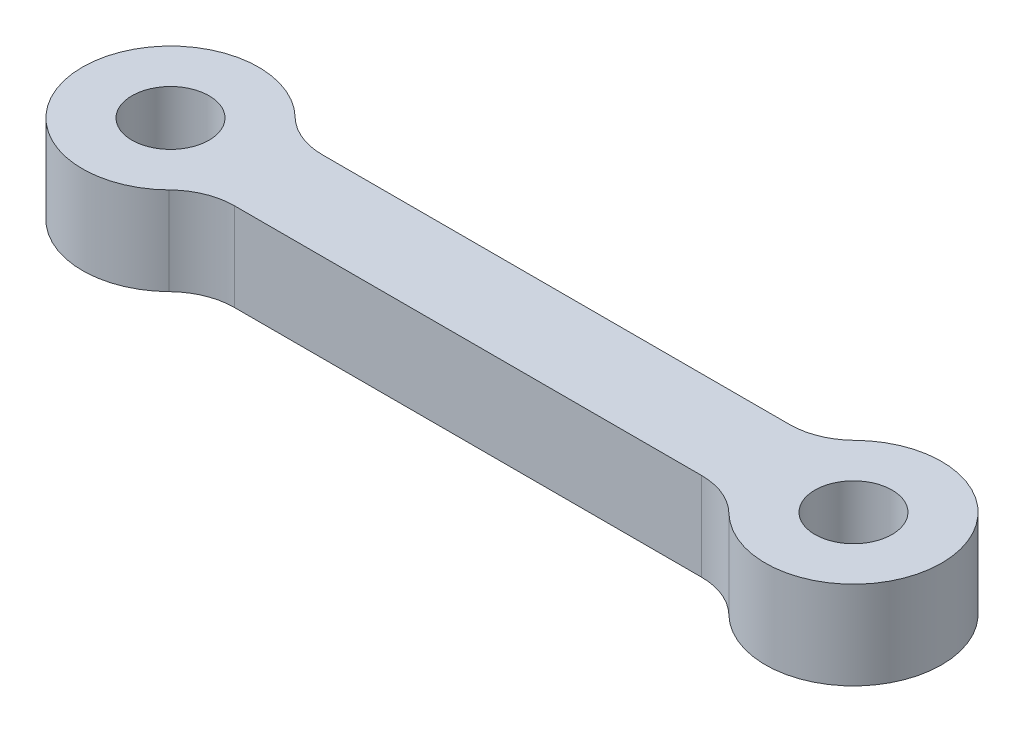
SolidWorks part; units mm, degrees
ref_plane "Front Plane" through (0, 0, 0) normal (0, 0, 1) x (1, 0, 0)
ref_plane "Top Plane" through (0, 0, 0) normal (0, 1, 0) x (1, 0, 0)
ref_plane "Right Plane" through (0, 0, 0) normal (1, 0, 0) x (0, 0, -1)
sketch "Sketch1" plane through (0, 0, 0) normal (0, 1, 0) x (1, 0, 0)
  line L0 (0, 0) -> (31, 0) construction
  line L1 (3.4641, 2) -> (27.5359, 2)
  line L2 (3.4641, -2) -> (27.5359, -2)
  circle A0 centre (0, 0) radius 4
  circle A1 centre (0, 0) radius 1.75
  circle A2 centre (31, 0) radius 1.75
  circle A3 centre (31, 0) radius 4
  dimension "D1" = 3.5
  dimension "D2" = 8
  dimension "D3" = 31
  dimension "D4" = 4
extrude "Boss-Extrude1" add sketch "Sketch1" along normal blind 4
fillet "Fillet1" radius 3 4 edges at (27.5359, 2, 2) (3.4641, 2, -2) (27.5359, 2, -2) (3.4641, 2, 2)
